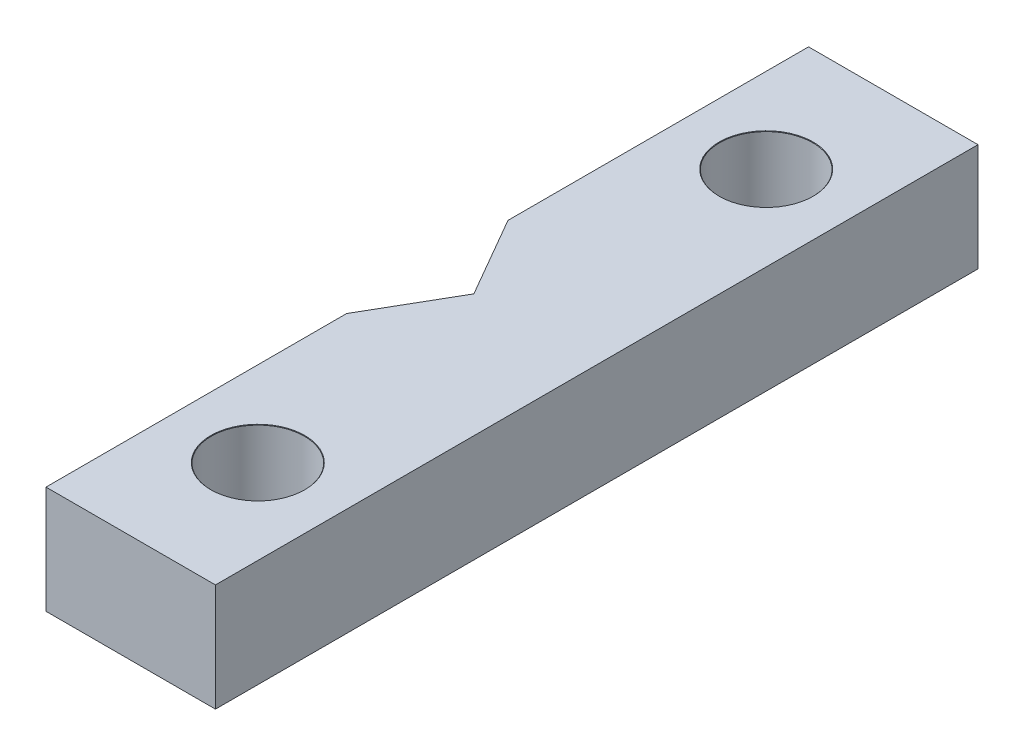
SolidWorks part; units mm, degrees
ref_plane "Front Plane" through (0, 0, 0) normal (0, 0, 1) x (1, 0, 0)
ref_plane "Top Plane" through (0, 0, 0) normal (0, 1, 0) x (1, 0, 0)
ref_plane "Right Plane" through (0, 0, 0) normal (1, 0, 0) x (0, 0, -1)
sketch "Sketch1" plane through (0, 0, 0) normal (0, 1, 0) x (1, 0, 0)
  line L0 (0.7494, 22.5) -> (10.7494, 22.5)
  line L1 (1.7494, 3.03) -> (-1.7494, 3.03)
  line L2 (-1.7494, 3.03) -> (-3.4987, 0)
  line L3 (-3.4987, 0) -> (-1.7494, -3.03)
  line L4 (-1.7494, -3.03) -> (1.7494, -3.03)
  line L5 (1.7494, -3.03) -> (3.4987, 0)
  line L6 (3.4987, 0) -> (1.7494, 3.03)
  line L13 (10.7494, 22.5) -> (10.7494, 7.5)
  line L15 (3.4987, 0) -> (10.7494, 0)
  line L16 (0.7494, -22.5) -> (10.7494, -22.5)
  line L17 (10.7494, -22.5) -> (10.7494, -7.5)
  line L18 (0.7494, -22.5) -> (0.7494, -4.7621)
  line L19 (0.7494, 4.7621) -> (0.7494, 22.5)
  line L22 (1.7494, 3.03) -> (0.7494, 4.7621)
  line L23 (1.7494, -3.03) -> (0.7494, -4.7621)
  line L24 (10.7494, 7.5) -> (10.7494, -7.5)
  circle A0 centre (0, 0) radius 3.03 construction
  dimension "D1" = 6.06
  dimension "D2" = 6.9975
  dimension "D3" = 10
  dimension "D4" = 15
extrude "Boss-Extrude1" add sketch "Sketch1" along normal blind 6.35
sketch "Sketch4" plane through (10.7494, 0, 0) normal (1, 0, 0) x (0, 0, -1)
  line L0 (-22.5, 0) -> (22.5, 0) construction
  line L1 (-22.5, 6.35) -> (-22.5, 0) construction
  line L2 (22.5, 6.35) -> (22.5, 0) construction
  point P0 (-15, 5)
  point P2 (15, 5)
  dimension "D1" = 5
  dimension "D2" = 7.5
  dimension "D3" = 7.5
hole_wizard "M5 Clearance Hole2" positions "Sketch7" profile "Sketch6" hole size "M5" standard "ANSI Metric"
sketch "Sketch7" [suppressed] plane through (0, 6.35, 0) normal (0, 1, 0) x (1, 0, 0)
  line L4 (10.7494, 22.5) -> (10.7494, -22.5) construction
  point P7 (5.7494, 15)
  point P9 (5.7494, -15)
  dimension "D1" = 5
  dimension "D2" = 15
sketch "Sketch6" plane through (5.7494, 6.35, -15) normal (1, 0, 0) x (0, 0, 1)
  line L0 (0, 0) -> (0, 11.7524)
  line L1 (0, 11.7524) -> (2.75, 10.1)
  line L2 (2.75, 10.1) -> (2.75, 0.025)
  line L3 (2.75, 0.025) -> (2.775, 0)
  line L5 (2.775, 0) -> (0, 0)
  line L6 (-2.75, 0.025) -> (-2.775, 0) construction
  line L10 (0, 11.7524) -> (-2.75, 10.1) construction
  line L11 (0, -6.35) -> (0, 107.95) construction
  dimension "Hole Dia." = 5.5
  dimension "Hole Depth" = 10.1
  dimension "Near C'Sink Dia." = 5.55
  dimension "Near C'Sink Angle" = 90
  dimension "Drill Angle" = 118
